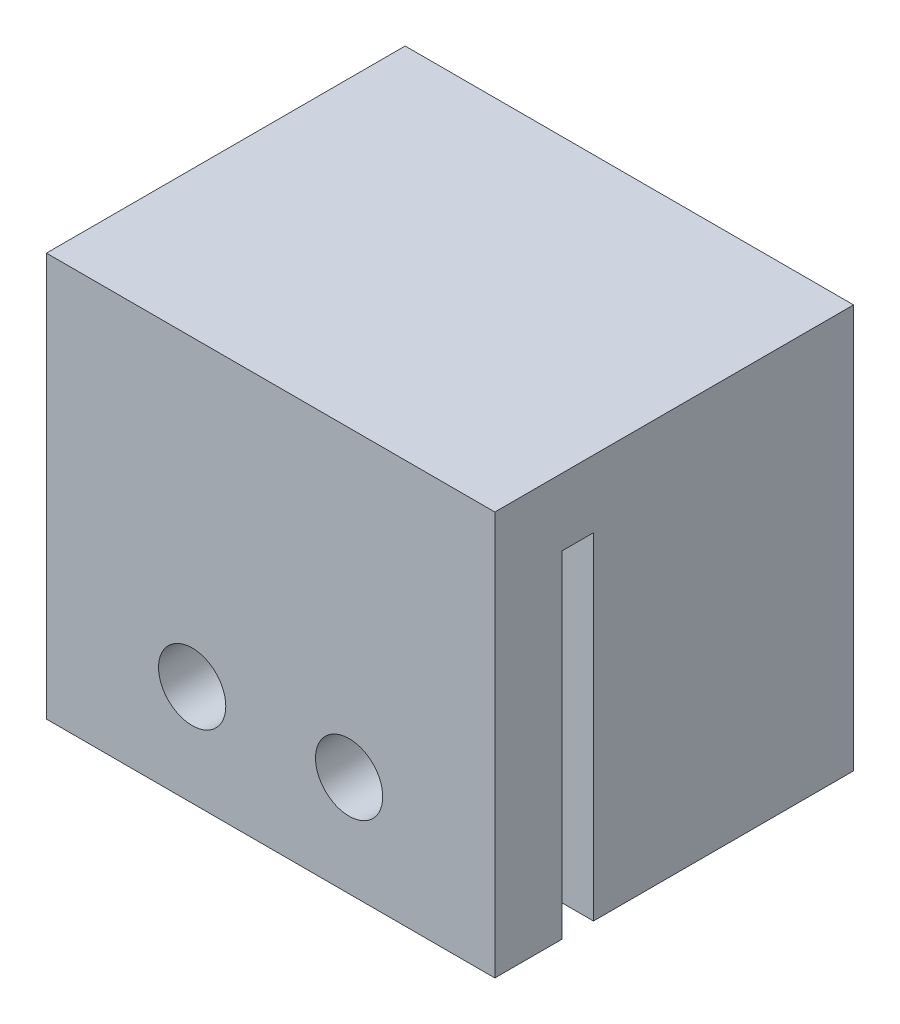
SolidWorks part; units mm, degrees
ref_plane "Alzado" through (0, 0, 0) normal (0, 0, 1) x (1, 0, 0)
ref_plane "Planta" through (0, 0, 0) normal (0, 1, 0) x (1, 0, 0)
ref_plane "Vista lateral" through (0, 0, 0) normal (1, 0, 0) x (0, 0, -1)
sketch "Croquis1" plane through (0, 0, 0) normal (0, 0, 1) x (1, 0, 0)
  line L1 (-10, -9) -> (10, -9)
  line L2 (-10, -9) -> (-10, 9)
  line L3 (-10, 9) -> (10, 9)
  line L4 (10, -9) -> (10, 9)
  line L5 (-10, -9) -> (10, 9) construction
  line L6 (-10, 9) -> (10, -9) construction
  point P0 (0, 0)
  dimension "D1" = 20
  dimension "D2" = 18
extrude "Saliente-Extruir1" add sketch "Croquis1" against normal blind 16
sketch "Croquis2" plane through (0, -9, 0) normal (0, -1, 0) x (1, 0, 0)
  line L0 (-10, -16) -> (10, -16) construction
  line L1 (-7.05, -16) -> (7.05, -16)
  line L2 (-7.05, -16) -> (-7.05, -4.4)
  line L3 (-7.05, -4.4) -> (7.05, -4.4)
  line L4 (7.05, -16) -> (7.05, -4.4)
  line L5 (0, -4.4) -> (0, 0) construction
  dimension "D1" = 14.1
  dimension "D2" = 4.4
extrude "Cortar-Extruir1" cut sketch "Croquis2" against normal blind 9.05
sketch "Croquis4" plane through (0, -9, 0) normal (0, -1, 0) x (1, 0, 0)
  line L0 (-10, -16) -> (-10, 0) construction
  line L1 (-10, -3) -> (10, -3)
  line L2 (-10, -3) -> (-10, -4.4)
  line L3 (-10, -4.4) -> (10, -4.4)
  line L4 (10, -3) -> (10, -4.4)
  line L5 (10, -16) -> (10, 0) construction
  line L6 (7.05, -4.4) -> (-7.05, -4.4) construction
  dimension "D1" = 1.4
extrude "Cortar-Extruir2" cut sketch "Croquis4" against normal blind 15
sketch "Croquis5" plane through (0, 0, 0) normal (0, 0, 1) x (1, 0, 0)
  circle A0 centre (-3.5, -4.5) radius 1.5
  circle A1 centre (3.5, -4.5) radius 1.5
  circle A2 centre (-3.5, -4.5) radius 2.675 construction
  circle A3 centre (3.5, -4.5) radius 2.675 construction
  dimension "D1" = 3
extrude "Cortar-Extruir3" cut sketch "Croquis5" against normal through all
